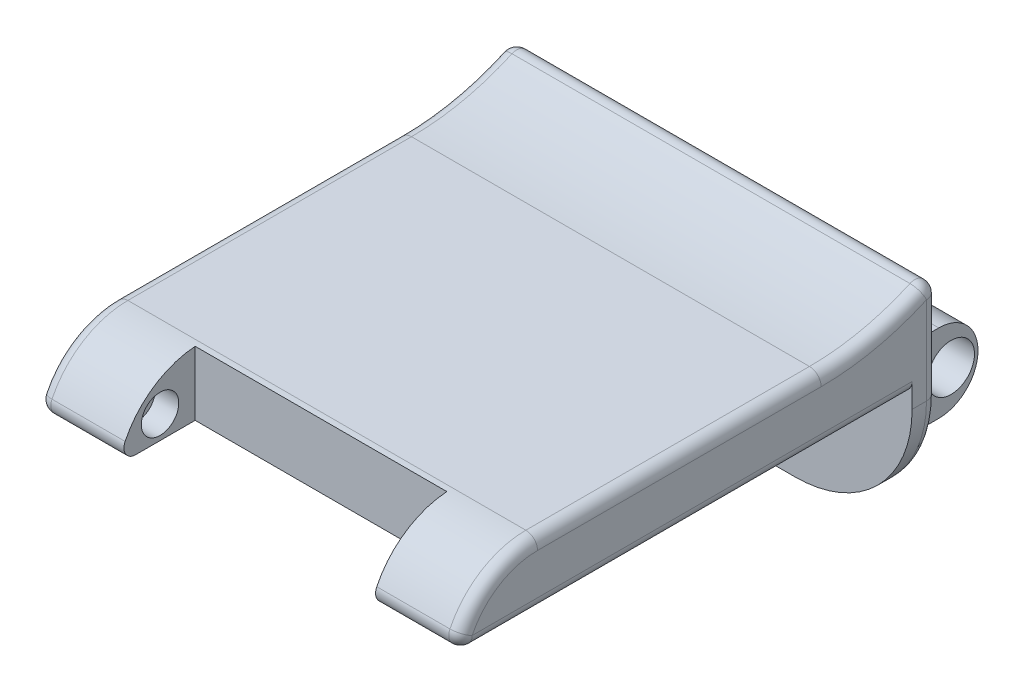
SolidWorks part; units mm, degrees
ref_plane "Front Plane" through (0, 0, 0) normal (0, 0, 1) x (1, 0, 0)
ref_plane "Top Plane" through (0, 0, 0) normal (0, 1, 0) x (1, 0, 0)
ref_plane "Right Plane" through (0, 0, 0) normal (1, 0, 0) x (0, 0, -1)
sketch "Sketch1" plane through (0, 0, 0) normal (1, 0, 0) x (0, 0, -1)
  line L0 (-16.23, 0) -> (22.77, 0)
  line L1 (22.77, 0) -> (22.77, -11.06)
  line L2 (22.77, -11.06) -> (25, -11.06)
  line L3 (25, -11.06) -> (25, 8.04)
  line L4 (-9.23, 5.5) -> (15, 5.5)
  arc A0 (15, 5.5) -> (25, 8.04) centre (15, 26.455) ccw
  arc A1 (-9.23, 5.5) -> (-16.23, 0) centre (-9.23, -1.7045) ccw
  dimension "D1" = 39
  dimension "D2" = 19.1
  dimension "D3" = 11.06
  dimension "D4" = 5.5
  dimension "D5" = 7
  dimension "D6" = 2.23
  dimension "D7" = 25
  dimension "D8" = 10
extrude "Boss-Extrude1" add sketch "Sketch1" along normal mid plane 36
sketch "Sketch2" plane through (0, 5.5, 0) normal (0, 1, 0) x (1, 0, 0)
  line L0 (18, -16.23) -> (-18, -16.23) construction
  line L1 (-10.75, -16.23) -> (10.75, -16.23)
  line L2 (-10.75, -16.23) -> (-10.75, -9.73)
  line L3 (-10.75, -9.73) -> (10.75, -9.73)
  line L4 (10.75, -16.23) -> (10.75, -9.73)
  line L5 (0, 6.3934) -> (0, -3.0955) construction
  dimension "D1" = 6.5
  dimension "D2" = 21.5
extrude "Cut-Extrude1" cut sketch "Sketch2" against normal blind 36
fillet "Fillet1" radius 1 1 edges at (0, 8.04, -25)
fillet "Fillet2" radius 10 2 edges at (-18, -11.06, -23.885) (18, -11.06, -23.885)
sketch "Sketch3" plane through (-10.75, 0, 0) normal (1, 0, 0) x (0, 0, -1)
  circle A0 centre (-12.73, 1.9826) radius 1.6
  dimension "D3" = 3.2
  dimension "D1" = 3.5
  dimension "D2" = 3.5
extrude "Cut-Extrude2" cut sketch "Sketch3" against normal blind 2 and the other way blind 23
sketch "Sketch4" plane through (0, 0, -25) normal (0, 0, -1) x (-1, 0, 0)
  line L0 (0, 3.2487) -> (0, -1.7938) construction
  line L1 (-15.8, 1.6295) -> (-4, 1.6295)
  line L2 (-15.8, 1.6295) -> (-15.8, -5.0705)
  line L3 (-15.8, -5.0705) -> (-4, -5.0705)
  line L4 (-4, 1.6295) -> (-4, -5.0705)
  line L5 (4, 1.6295) -> (15.8, 1.6295)
  line L6 (4, 1.6295) -> (4, -5.0705)
  line L7 (4, -5.0705) -> (15.8, -5.0705)
  line L8 (15.8, 1.6295) -> (15.8, -5.0705)
  line L9 (18, 6.4295) -> (-18, 6.4295) construction
  dimension "D1" = 11.8
  dimension "D2" = 8
  dimension "D3" = 6.7
  dimension "D4" = 4.8
extrude "Boss-Extrude2" add sketch "Sketch4" along normal blind 5.6
sketch "Sketch5" plane through (15.8, 0, 0) normal (1, 0, 0) x (0, 0, -1)
  line L0 (30.6, 1.6295) -> (30.6, -5.0705) construction
  line L1 (30.6, 1.6295) -> (25, 1.6295) construction
  line L2 (30.6, -5.0705) -> (25, -5.0705) construction
  line L3 (30.6, 1.6295) -> (27.25, 1.6295)
  line L4 (30.6, 1.6295) -> (30.6, -5.0705)
  line L5 (30.6, -5.0705) -> (27.25, -5.0705)
  arc A0 (27.25, -5.0705) -> (27.25, 1.6295) centre (27.25, -1.7205) ccw
  line M2 (25, -5.0705) -> (30.6, -5.0705)
  line M3 (30.6, -5.0705) -> (30.6, 1.6295)
  line M4 (30.6, 1.6295) -> (25, 1.6295)
extrude "Cut-Extrude3" cut sketch "Sketch5" against normal through all contours A0 L4 M4 | A0 M2 M3
sketch "Sketch6" plane through (15.8, 0, 0) normal (1, 0, 0) x (0, 0, -1)
  line L0 (27.25, 1.6295) -> (25, 1.6295) construction
  circle A0 centre (28.3022, -1.8205) radius 2
  arc A1 (27.25, -5.0705) -> (27.25, 1.6295) centre (27.25, -1.7205) ccw construction
  point P3 (30.6, -1.7205)
  dimension "D1" = 4
  dimension "D2" = 2.3
  dimension "D3" = 3.45
extrude "Cut-Extrude4" cut sketch "Sketch6" against normal through all
sketch "Sketch7" plane through (0, 0, 0) normal (0, -1, 0) x (1, 0, 0)
  line L0 (0, 2.9646) -> (0, -2.259) construction
  line L1 (-16.61, 8.63) -> (16.61, 8.63)
  line L2 (-16.61, 8.63) -> (-16.61, -15.57)
  line L3 (-16.61, -15.57) -> (16.61, -15.57)
  line L4 (16.61, 8.63) -> (16.61, -15.57)
  line L5 (-16.61, 8.63) -> (16.61, -15.57) construction
  line L6 (-16.61, -15.57) -> (16.61, 8.63) construction
  line L7 (18, -22.77) -> (-18, -22.77) construction
  point P0 (0, -3.47)
  dimension "D1" = 33.22
  dimension "D2" = 24.2
  dimension "D3" = 7.2
extrude "Cut-Extrude5" cut sketch "Sketch7" against normal blind 1
sketch "Sketch8" plane through (0, 1, 0) normal (0, -1, 0) x (1, 0, 0)
  line L0 (0, 2.3034) -> (0, -3.1186) construction
  line L1 (18, -22.77) -> (-18, -22.77) construction
  point P0 (-9.7, -5.27)
  point P1 (9.7, -5.27)
  dimension "D1" = 19.4
  dimension "D2" = 17.5
hole_wizard "M1.6 Tapped Hole1" positions "Sketch10" profile "Sketch9" tap size "M1.6" standard "ISO"
sketch "Sketch10" plane through (0, 1, 0) normal (0, -1, 0) x (-1, 0, 0)
  point P0 (9.7, 5.27)
  point P3 (-9.7, 5.27)
sketch "Sketch9" plane through (-9.7, 1, -5.27) normal (1, 0, 0) x (0, 0, -1)
  line L0 (0, 0) -> (0, 3.3755)
  line L1 (0, 3.3755) -> (0.625, 3)
  line L2 (0.625, 3) -> (0.625, 0)
  line L5 (0.625, 0) -> (0, 0)
  line L10 (0, 3.3755) -> (-0.625, 3) construction
  line L11 (0, -6.35) -> (0, 107.95) construction
  dimension "Tap Drill Dia." = 1.25
  dimension "Tap Drill Depth" = 3
  dimension "Drill Angle" = 118
cosmetic thread "Hole Thread1" parameters "D1"=3, "D2"=1.6
cosmetic thread "Hole Thread2" parameters "D1"=3, "D2"=1.6
fillet "Fillet3" radius 1 2 edges at (-14.375, 0, 16.23) (14.375, 0, 16.23)
fillet "Fillet4" radius 1 17 edges at (-18, 0, -3.978) (-18, 0.4689, 15.6614) (-18, 4.4, 13.0562) (-18, 5.5, -2.885) (-18, 5.9656, -19.3926) (-18, 7.2691, -24.5432) (-18, 2.6847, -25) (-15.0711, -8.1311, -25) (0, -11.06, -25) (15.0711, -8.1311, -25) (18, 2.6847, -25) (18, 7.2691, -24.5432) (18, 5.9656, -19.3926) (18, 0, -3.978) (18, 0.4689, 15.6614) (18, 4.4, 13.0562) (18, 5.5, -2.885)
